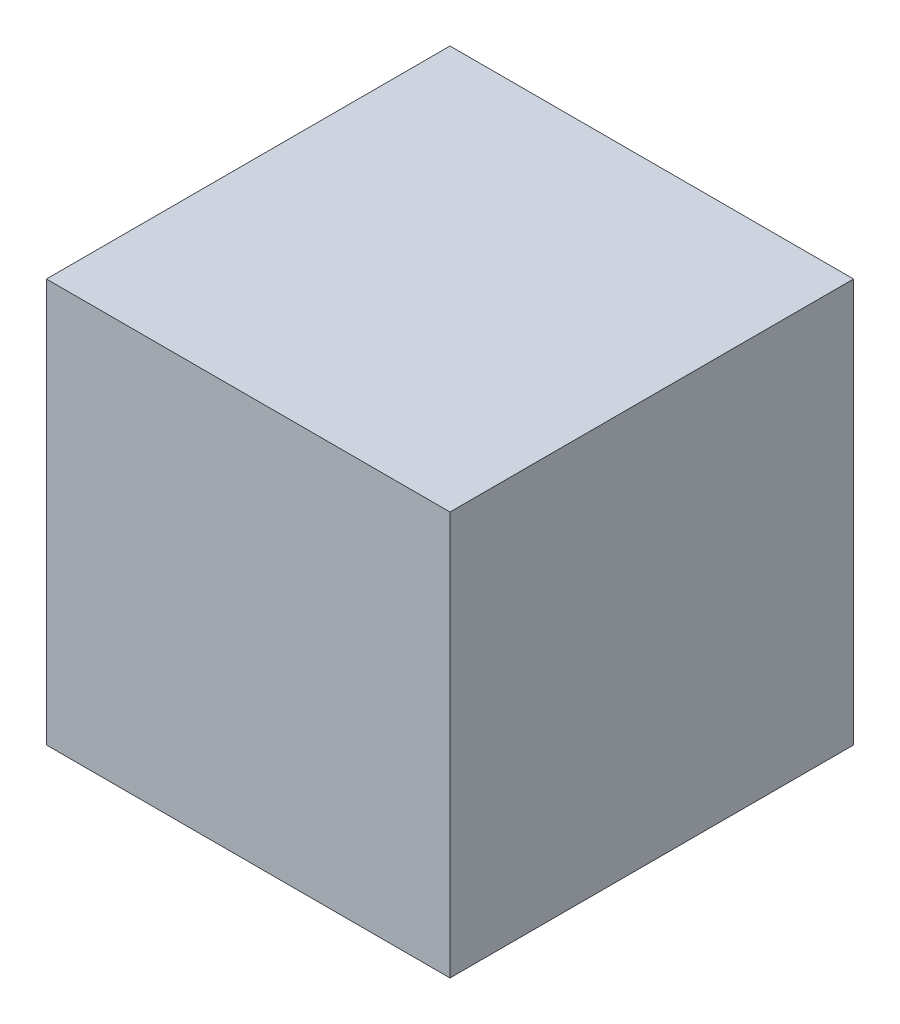
SolidWorks part; units mm, degrees
material "Простая углеродистая сталь"
ref_plane "Спереди" through (0, 0, 0) normal (0, 0, 1) x (1, 0, 0)
ref_plane "Сверху" through (0, 0, 0) normal (0, 1, 0) x (1, 0, 0)
ref_plane "Справа" through (0, 0, 0) normal (1, 0, 0) x (0, 0, -1)
sketch "Эскиз1" plane through (0, 0, 0) normal (0, 1, 0) x (1, 0, 0)
  line L1 (-5, 5) -> (5, 5)
  line L2 (-5, 5) -> (-5, -5)
  line L3 (-5, -5) -> (5, -5)
  line L4 (5, 5) -> (5, -5)
  point P4 (0, 5)
  point P5 (-5, 0)
  dimension "D1" = 10
extrude "Бобышка-Вытянуть1" add sketch "Эскиз1" along normal mid plane 10
equation "\"Площадь в метрах квадратных\"= \"Площадь\" / 1000000"
